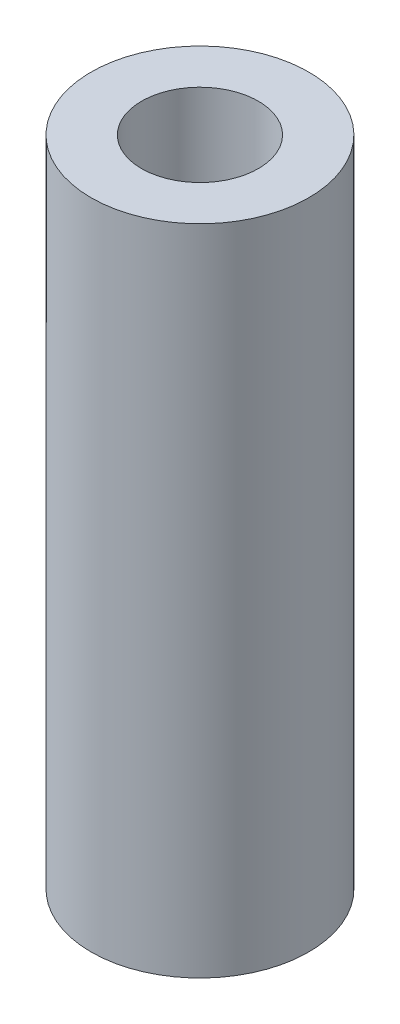
SolidWorks part; units mm, degrees
material "6061-T6 (SS)"
ref_plane "Front Plane" through (0, 0, 0) normal (0, 0, 1) x (1, 0, 0)
ref_plane "Top Plane" through (0, 0, 0) normal (0, 1, 0) x (1, 0, 0)
ref_plane "Right Plane" through (0, 0, 0) normal (1, 0, 0) x (0, 0, -1)
sketch "Sketch1" plane through (0, 0, 0) normal (0, 1, 0) x (1, 0, 0)
  circle A0 centre (0, 0) radius 1.5875
  circle A1 centre (0, 0) radius 0.8521
  dimension "D1" = 3.175
extrude "Boss-Extrude1" add sketch "Sketch1" along normal blind 9.525 contours A0 A1
